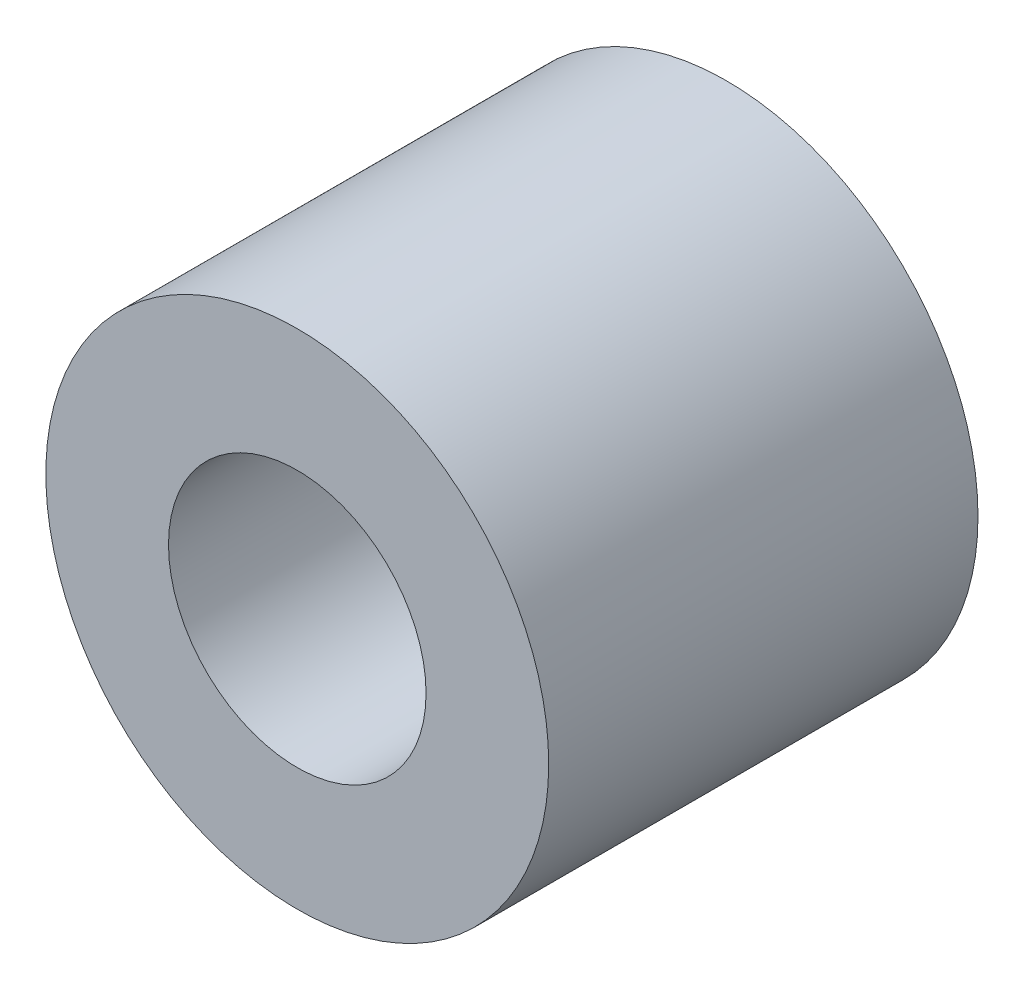
SolidWorks part; units mm, degrees
ref_plane "Front Plane" through (0, 0, 0) normal (0, 0, 1) x (1, 0, 0)
ref_plane "Top Plane" through (0, 0, 0) normal (0, 1, 0) x (1, 0, 0)
ref_plane "Right Plane" through (0, 0, 0) normal (1, 0, 0) x (0, 0, -1)
sketch "Sketch2" plane through (0, 0, 0) normal (0, 0, 1) x (1, 0, 0)
  circle A0 centre (0, 0) radius 3.15
  circle A1 centre (0, 0) radius 6.15
  dimension "D1" = 6.3
  dimension "D2" = 3
extrude "Boss-Extrude1" add sketch "Sketch2" along normal blind 10.5
